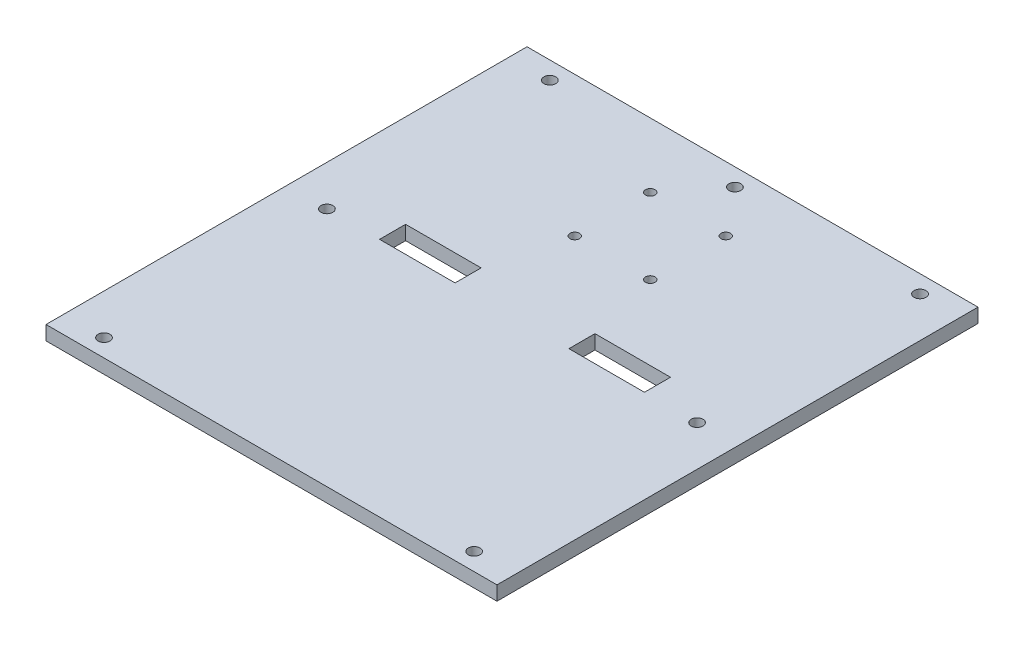
SolidWorks part; units mm, degrees
material "Acrylic (Medium-high impact)"
ref_plane "Front Plane" through (0, 0, 0) normal (0, 0, 1) x (1, 0, 0)
ref_plane "Top Plane" through (0, 0, 0) normal (0, 1, 0) x (1, 0, 0)
ref_plane "Right Plane" through (0, 0, 0) normal (1, 0, 0) x (0, 0, -1)
sketch "Sketch2" plane through (0, 0, 0) normal (0, 1, 0) x (1, 0, 0)
  line L1 (-95.25, 101.6) -> (95.25, 101.6)
  line L2 (-95.25, 101.6) -> (-95.25, -101.6)
  line L3 (-95.25, -101.6) -> (95.25, -101.6)
  line L4 (95.25, 101.6) -> (95.25, -101.6)
  line L5 (-95.25, 101.6) -> (95.25, -101.6) construction
  line L6 (-95.25, -101.6) -> (95.25, 101.6) construction
  point P0 (0, 0)
extrude "Boss-Extrude1" add sketch "Sketch2" along normal blind 6
sketch "Sketch5" plane through (0, 6, 0) normal (0, 1, 0) x (1, 0, 0)
  line L0 (-78.187, 101.6) -> (-78.187, 86.7301)
  line L1 (95.25, 101.6) -> (-95.25, 101.6) construction
  line L2 (-78.187, 94.1651) -> (-95.25, 94.1651)
  line L3 (-95.25, 101.6) -> (-95.25, -101.6) construction
  line L4 (0, 101.6) -> (0, -101.6)
  line L5 (-95.25, -101.6) -> (95.25, -101.6) construction
  line L6 (0, 0) -> (-95.25, 0)
  line L7 (0, 0) -> (95.25, 0)
  line L8 (95.25, -101.6) -> (95.25, 101.6) construction
  circle A0 centre (-78.187, 94.1651) radius 2.5
  circle A1 centre (78.187, 94.1651) radius 2.5
  circle A2 centre (-78.187, -94.1651) radius 2.5
  circle A3 centre (78.187, -94.1651) radius 2.5
  circle A4 centre (-78.187, 0) radius 2.5
  circle A5 centre (78.187, 0) radius 2.5
  circle A7 centre (0, 94.1651) radius 2.5
extrude "Cut-Extrude6" cut sketch "Sketch5" against normal through all
sketch "Sketch6" plane through (0, 6, 0) normal (0, 1, 0) x (1, 0, 0)
  line L0 (-95.25, 0) -> (95.25, 0)
  line L1 (-95.25, 101.6) -> (95.25, 101.6)
  line L2 (-95.25, 101.6) -> (-95.25, -101.6)
  line L3 (-95.25, -101.6) -> (95.25, -101.6)
  line L4 (95.25, 101.6) -> (95.25, -101.6)
  line L5 (15.95, 42.45) -> (20, 42.45)
  line L6 (-15.95, 42.45) -> (-15.95, 0)
  line L7 (-15.95, 42.45) -> (15.95, 42.45)
  line L8 (-15.95, 42.45) -> (-15.95, 74.35)
  line L9 (-15.95, 74.35) -> (15.95, 74.35)
  line L10 (15.95, 42.45) -> (15.95, 74.35)
  line L11 (-15.95, 42.45) -> (15.95, 74.35) construction
  line L12 (-15.95, 74.35) -> (15.95, 42.45) construction
  line L13 (-30, 88.4) -> (30, 88.4) construction
  line L14 (-30, 88.4) -> (-30, 28.4) construction
  line L15 (-30, 28.4) -> (30, 28.4) construction
  line L16 (30, 88.4) -> (30, 28.4) construction
  line L17 (-30, 88.4) -> (30, 28.4) construction
  line L18 (-30, 28.4) -> (30, 88.4) construction
  line L19 (-20, 78.4) -> (20, 78.4)
  line L20 (-20, 78.4) -> (-20, 38.4)
  line L21 (-20, 38.4) -> (20, 38.4)
  line L22 (20, 78.4) -> (20, 38.4)
  line L23 (-20, 78.4) -> (20, 38.4) construction
  line L24 (-20, 38.4) -> (20, 78.4) construction
  line L25 (20, 42.45) -> (20, 0)
  line L27 (20, 0) -> (40, 0)
  line L32 (0, -3.3) -> (0, 3.3) construction
  line L33 (40, 11) -> (55.95, 11)
  line L34 (55.95, 11) -> (55.95, 0)
  line L35 (55.95, 0) -> (20, 0)
  line L36 (40, 11) -> (24.05, 11)
  line L37 (24.05, 11) -> (24.05, 0)
  line L38 (-24.05, 11) -> (-24.05, 0)
  line L39 (-55.95, 11) -> (-55.95, 0)
  line L40 (-40, 11) -> (-55.95, 11)
  line L41 (-40, 11) -> (-24.05, 11)
  circle A0 centre (-15.95, 74.35) radius 2
  circle A1 centre (15.95, 74.35) radius 2
  circle A2 centre (15.95, 42.45) radius 2
  circle A3 centre (-15.95, 42.45) radius 2
  point P11 (0, 58.4)
  point P16 (0, 58.4)
  point P25 (0, 58.4)
  dimension "D5" = 40
  dimension "D1" = 31.9
  dimension "D2" = 31.9
  dimension "D3" = 60
  dimension "D4" = 60
  dimension "D6" = 40
extrude "Cut-Extrude7" cut sketch "Sketch6" against normal blind 10 contours L9 A0 L8 | L10 A1 L9 | L9 A1 L10 | L7 A3 L8 | L8 A3 L6 | L10 A2 L7 | L5 A2 L10 | L7 A2 L5 | L6 A3 L7 | L41 L40 L39 L0 L38 | L36 L37 L35 L0 L34 L33
